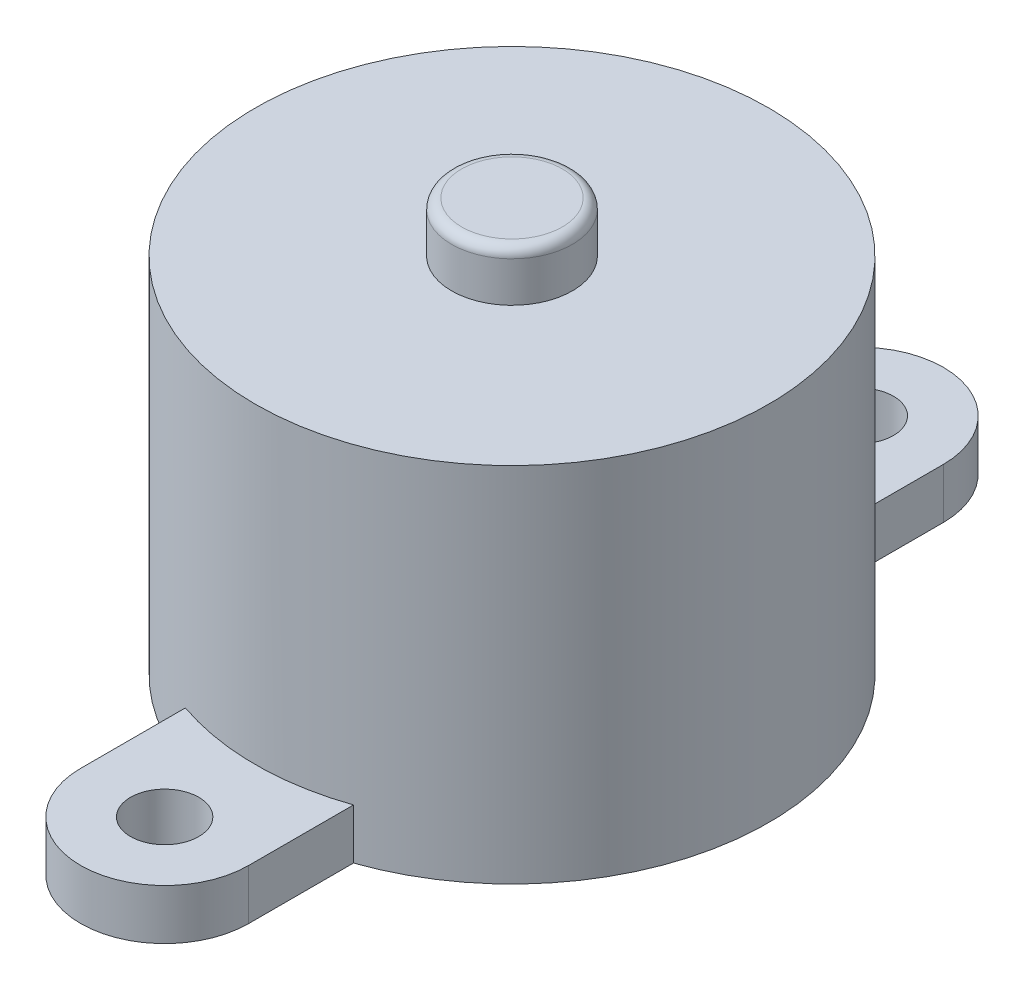
SolidWorks part; units mm, degrees
ref_plane "Front Plane" through (0, 0, 0) normal (0, 0, 1) x (1, 0, 0)
ref_plane "Top Plane" through (0, 0, 0) normal (0, 1, 0) x (1, 0, 0)
ref_plane "Right Plane" through (0, 0, 0) normal (1, 0, 0) x (0, 0, -1)
sketch "Sketch1" plane through (0, 0, 0) normal (0, 1, 0) x (1, 0, 0)
  circle A0 centre (0, 0) radius 12.75
  dimension "D1" = 25.5
extrude "Boss-Extrude1" add sketch "Sketch1" along normal blind 18
sketch "Sketch2" plane through (0, 18, 0) normal (0, 1, 0) x (1, 0, 0)
  circle A0 centre (0, 0) radius 3
  dimension "D1" = 6
extrude "Boss-Extrude2" add sketch "Sketch2" along normal blind 2.5
fillet "Fillet1" radius 0.5 1 edges at (0, 20.5, 3)
sketch "Sketch3" plane through (0, 0, 0) normal (0, 1, 0) x (1, 0, 0)
  line L0 (4.175, 12.0471) -> (4.175, 17.2524)
  line L1 (-4.175, 12.0471) -> (-4.175, 17.2524)
  line L2 (0, -11.275) -> (0, 11.275) construction
  line L3 (-4.175, 12.0471) -> (4.175, 12.0471)
  circle A0 centre (0, 0) radius 12.75 construction
  arc A1 (-4.175, 17.2524) -> (4.175, 17.2524) centre (0, 17.2524) cw
  circle A2 centre (0, 17.2524) radius 1.6934
  dimension "D3" = 17.2524
  dimension "D1" = 8.35
  dimension "D2" = 4.175
extrude "Boss-Extrude3" add sketch "Sketch3" along normal blind 2.5
mirror "Mirror1" about plane through (0, 0, 0) normal (0, 0, 1) of "Boss-Extrude3"
